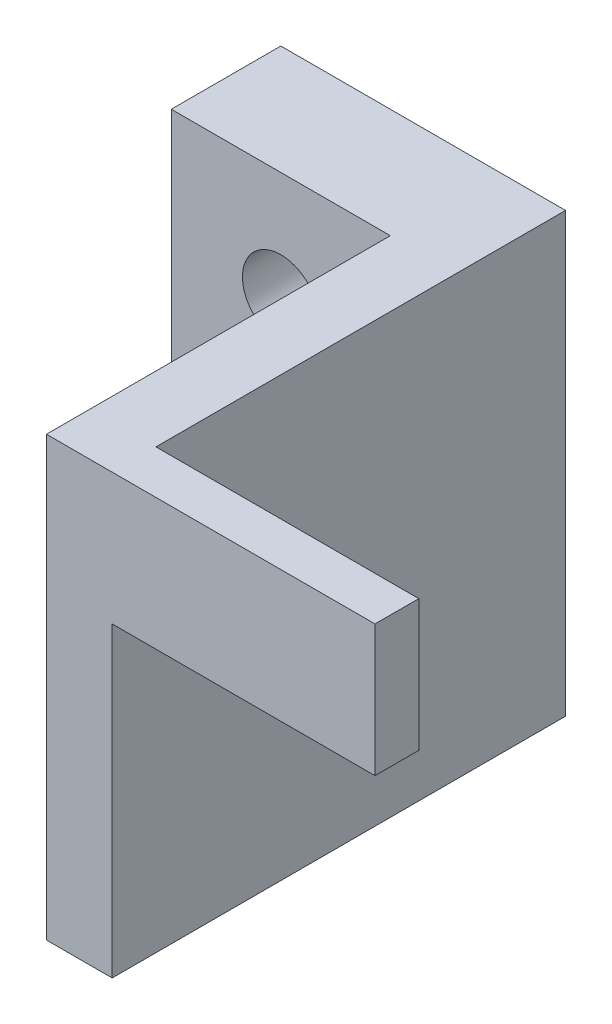
SolidWorks part; units mm, degrees
ref_plane "前视基准面" through (0, 0, 0) normal (0, 0, 1) x (1, 0, 0)
ref_plane "上视基准面" through (0, 0, 0) normal (0, 1, 0) x (1, 0, 0)
ref_plane "右视基准面" through (0, 0, 0) normal (1, 0, 0) x (0, 0, -1)
sketch "草图1" plane through (0, 0, 0) normal (0, 0, 1) x (1, 0, 0)
  line L1 (0, 0) -> (13, 0)
  line L2 (0, 0) -> (0, 20)
  line L3 (0, 20) -> (13, 20)
  line L4 (13, 0) -> (13, 20)
  dimension "D1" = 13
  dimension "D2" = 20
extrude "凸台-拉伸1" add sketch "草图1" along normal blind 5
sketch "草图3" plane through (0, 0, 5) normal (0, 0, 1) x (1, 0, 0)
  line L0 (0, 0) -> (13, 0) construction
  line L1 (13, 20) -> (10, 20)
  line L2 (13, 20) -> (13, 0)
  line L3 (13, 0) -> (10, 0)
  line L4 (10, 20) -> (10, 0)
  dimension "D1" = 3
extrude "凸台-拉伸2" add sketch "草图3" along normal blind 15.7
sketch "草图4" plane through (10, 0, 0) normal (-1, 0, 0) x (0, 0, 1)
  line L0 (20.7, 0) -> (5, 0) construction
  line L1 (20.7, 20) -> (18.7, 20)
  line L2 (20.7, 20) -> (20.7, 0)
  line L3 (20.7, 0) -> (18.7, 0)
  line L4 (18.7, 20) -> (18.7, 0)
  dimension "D1" = 2
extrude "凸台-拉伸3" add sketch "草图4" against normal blind 15
sketch "草图5" plane through (0, 0, 20.7) normal (0, 0, 1) x (1, 0, 0)
  line L0 (10, 20) -> (10, 0) construction
  line L1 (25, 0) -> (13, 0)
  line L2 (25, 0) -> (25, 14)
  line L3 (25, 14) -> (13, 14)
  line L4 (13, 0) -> (13, 14)
  line L5 (25, 20) -> (10, 20) construction
  dimension "D1" = 3
  dimension "D2" = 6
extrude "切除-拉伸1" cut sketch "草图5" against normal through all
sketch "草图6" plane through (0, 0, 5) normal (0, 0, 1) x (1, 0, 0)
  line L0 (0, 10) -> (10, 10) construction
  line L1 (0, 20) -> (0, 0) construction
  line L2 (10, 20) -> (10, 0) construction
  line L3 (10, 10) -> (5, 10) construction
  line L4 (5, 10) -> (5, 26.783) construction
  circle A0 centre (5, 15) radius 1.75
  circle A1 centre (5, 5) radius 1.75
  dimension "D1" = 3.5
  dimension "D2" = 10
extrude "切除-拉伸2" cut sketch "草图6" against normal through all
